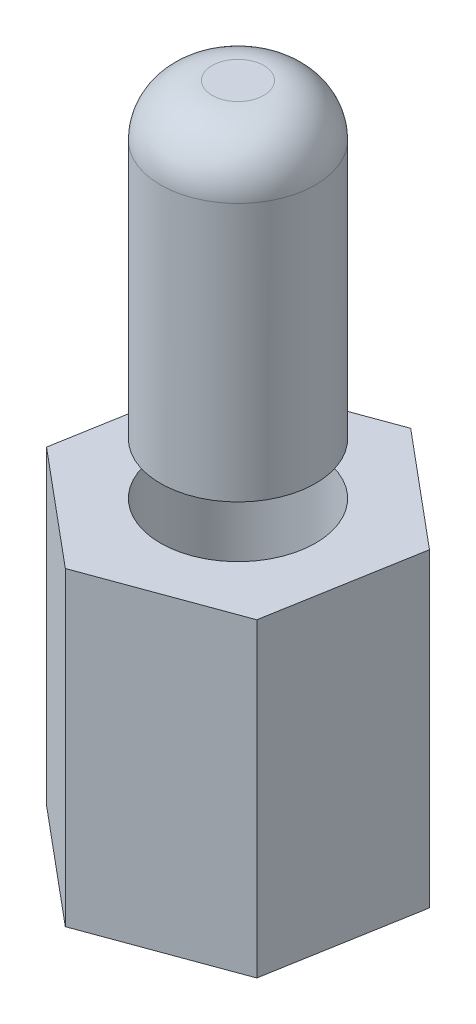
SolidWorks part; units mm, degrees
ref_plane "Front Plane" through (0, 0, 0) normal (0, 0, 1) x (1, 0, 0)
ref_plane "Top Plane" through (0, 0, 0) normal (0, 1, 0) x (1, 0, 0)
ref_plane "Right Plane" through (0, 0, 0) normal (1, 0, 0) x (0, 0, -1)
sketch "Sketch1" plane through (0, 0, 0) normal (0, 1, 0) x (1, 0, 0)
  line L1 (2.2148, -1.8515) -> (2.7108, 0.9924)
  line L2 (2.7108, 0.9924) -> (0.496, 2.8438)
  line L3 (0.496, 2.8438) -> (-2.2148, 1.8515)
  line L4 (-2.2148, 1.8515) -> (-2.7108, -0.9924)
  line L5 (-2.7108, -0.9924) -> (-0.496, -2.8438)
  line L6 (-0.496, -2.8438) -> (2.2148, -1.8515)
  circle A0 centre (0, 0) radius 2.5 construction
  dimension "D1" = 5
extrude "Boss-Extrude1" add sketch "Sketch1" along normal blind 6
sketch "Sketch2" plane through (0, 6, 0) normal (0, 1, 0) x (1, 0, 0)
  circle A0 centre (0, 0) radius 1.5
  dimension "D1" = 3
extrude "Boss-Extrude2" add sketch "Sketch2" along normal blind 7
sketch "Sketch3" plane through (0, 0, 0) normal (0, -1, 0) x (1, 0, 0)
  circle A0 centre (0, 0) radius 1.5
extrude "Cut-Extrude1" cut sketch "Sketch3" against normal blind 7
fillet "Fillet1" radius 1 1 edges at (0, 13, 1.5)
